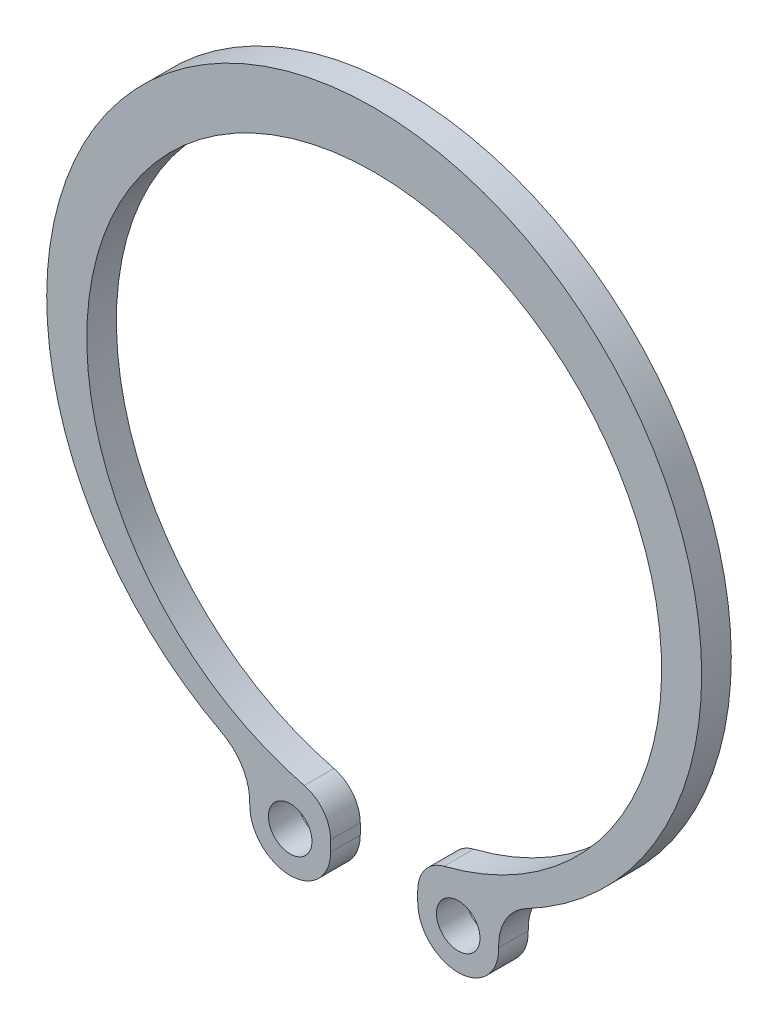
SolidWorks part; units mm, degrees
material "AISI Тип A2 Инструментальная сталь"
ref_plane "Спереди" through (0, 0, 0) normal (0, 0, 1) x (1, 0, 0)
ref_plane "Сверху" through (0, 0, 0) normal (0, 1, 0) x (1, 0, 0)
ref_plane "Справа" through (0, 0, 0) normal (1, 0, 0) x (0, 0, -1)
sketch "Эскиз1" plane through (0, 0, 0) normal (0, 0, 1) x (1, 0, 0)
  line L0 (0, -1000) -> (0, 49000) construction
  line L1 (-2.5, -19.4614) -> (-2.5, -18.8444)
  line L2 (2.5, -19.4614) -> (2.5, -18.8444)
  arc A0 (8.7465, -16.6415) -> (-8.7465, -16.6415) centre (0, 0) ccw
  arc A1 (4.0135, -16.9044) -> (-4.0135, -16.9044) centre (0, -0.9) ccw
  circle A2 centre (-4.8224, -19.4614) radius 1.25
  arc A3 (-7.1436, -19.3897) -> (-2.5, -19.4614) centre (-4.8224, -19.4614) ccw
  arc A4 (-4.0135, -16.9044) -> (-2.5, -18.8444) centre (-4.5, -18.8444) cw
  arc A5 (-8.7465, -16.6415) -> (-7.1436, -19.3897) centre (-10.1422, -19.2971) cw
  arc A6 (8.7465, -16.6415) -> (7.1436, -19.3897) centre (10.1422, -19.2971) ccw
  arc A7 (4.0135, -16.9044) -> (2.5, -18.8444) centre (4.5, -18.8444) ccw
  arc A8 (7.1436, -19.3897) -> (2.5, -19.4614) centre (4.8224, -19.4614) cw
  circle A9 centre (4.8224, -19.4614) radius 1.25
  point P17 (-2.5, -17.2095)
  dimension "D2" = 37.6
  dimension "D3" = 33
  dimension "D4" = 2.5
  dimension "D5" = 2
  dimension "D6" = 3
  dimension "D7" = 5
  dimension "D8" = 5
  dimension "D1" = 0.9
extrude "Бобышка-Вытянуть1" add sketch "Эскиз1" along normal blind 1.7
